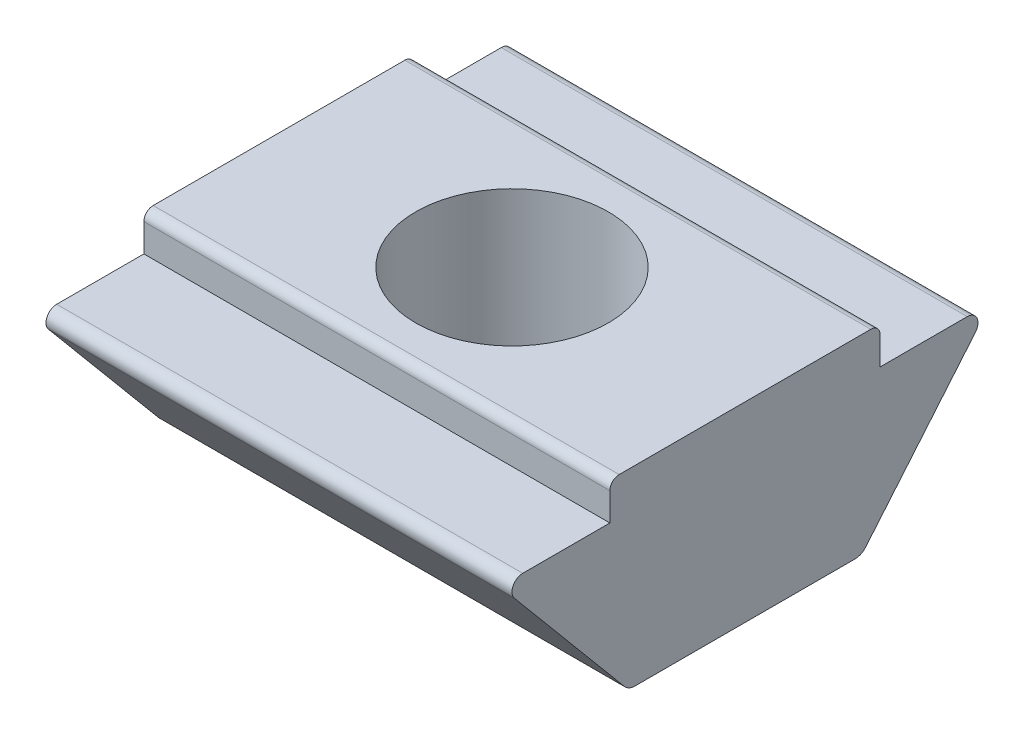
SolidWorks part; units mm, degrees
ref_plane "Front Plane" through (0, 0, 0) normal (0, 0, 1) x (1, 0, 0)
ref_plane "Top Plane" through (0, 0, 0) normal (0, 1, 0) x (1, 0, 0)
ref_plane "Right Plane" through (0, 0, 0) normal (1, 0, 0) x (0, 0, -1)
ref_plane "Plane1" through (-5, 0, 0) normal (1, 0, 0) x (0, 0, -1)
sketch "Sketch1" plane through (-5, 0, 0) normal (1, 0, 0) x (0, 0, -1)
  line L0 (2.5, -4.1) -> (-2.5, -4.1)
  line L1 (-2.5, -4.1) -> (-4.9464, -1.1776)
  line L2 (-4.77, -0.8) -> (-2.9, -0.8)
  line L3 (-2.9, -0.8) -> (-2.9, 0)
  line L4 (-2.9, 0) -> (2.9, 0)
  line L5 (2.9, 0) -> (2.9, -0.8)
  line L6 (2.9, -0.8) -> (4.77, -0.8)
  line L7 (4.9464, -1.1776) -> (2.5, -4.1)
  line L8 (0, 0) -> (0, -4.1) construction
  line L9 (5, -4.1) -> (5, -0.8) construction
  line L10 (-5, -0.8) -> (-5, -4.1) construction
  arc A0 (-4.9464, -1.1776) -> (-4.77, -0.8) centre (-4.77, -1.03) cw
  arc A1 (4.77, -0.8) -> (4.9464, -1.1776) centre (4.77, -1.03) cw
  point P13 (-5.2625, -0.8)
  point P16 (5.2625, -0.8)
  dimension "FIX_5" = 0.23
  dimension "FIX_3" = 5.8
  dimension "E" = 3.3
  dimension "T" = 4.1
  dimension "FIX_2" = 10
  dimension "FIX_4" = 5
extrude "Boss-Extrude1" add sketch "Sketch1" along normal blind 10
fillet "Fillet1" radius 0.3 2 edges at (0, -4.1, 2.5) (0, -4.1, -2.5)
fillet "Fillet2" radius 0.2 2 edges at (0, 0, -2.9) (0, 0, 2.9)
hole_wizard "Tapped Hole1" positions "Sketch3" profile "Sketch2" tap size "M5x0.8" standard "JIS" end condition through all
sketch "Sketch3" plane through (0, 0, 0) normal (0, 1, 0) x (1, 0, 0)
  point P0 (0, 0)
cosmetic thread "Thread1"
sketch "Sketch2" plane through (0, 0, 0) normal (1, 0, 0) x (0, 0, 1)
  line L0 (0, 0) -> (0, 4.1)
  line L1 (0, 4.1) -> (2.067, 4.1)
  line L2 (2.067, 4.1) -> (2.067, 0)
  line L5 (2.067, 0) -> (0, 0)
  line L11 (0, 0) -> (0, 4.1) construction
  dimension "Thru Tap Drill Dia." = 4.134
  dimension "Thru Tap Drill Depth" = 4.1
